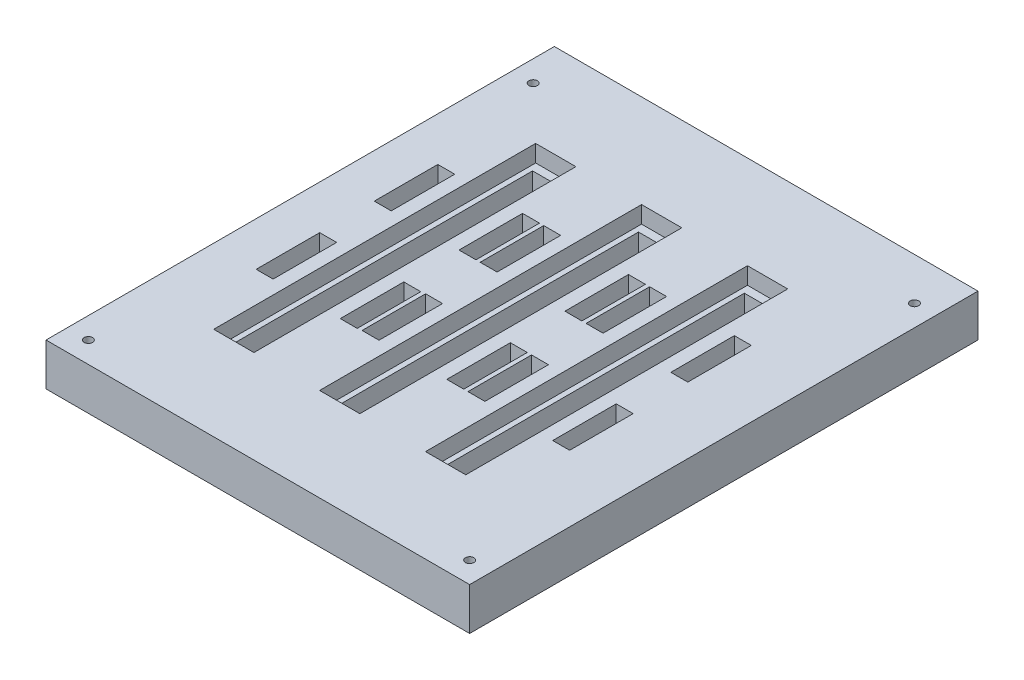
SolidWorks part; units mm, degrees
ref_plane "Front Plane" through (0, 0, 0) normal (0, 0, 1) x (1, 0, 0)
ref_plane "Top Plane" through (0, 0, 0) normal (0, 1, 0) x (1, 0, 0)
ref_plane "Right Plane" through (0, 0, 0) normal (1, 0, 0) x (0, 0, -1)
sketch "Sketch2" plane through (0, 0, 0) normal (0, 1, 0) x (1, 0, 0)
  line L0 (0, -60) -> (0, -36) construction
  line L1 (-50, -60) -> (50, -60)
  line L2 (-50, -60) -> (-50, 60)
  line L3 (-50, 60) -> (50, 60)
  line L4 (50, -60) -> (50, 60)
  line L5 (-50, -60) -> (-6.1463, -7.3755) construction
  line L6 (-50, 60) -> (-6.1463, 7.3755) construction
  line L7 (18.8537, 36) -> (25.8537, 36)
  line L8 (-6.1463, -36) -> (0.8537, -36)
  line L9 (-6.1463, -36) -> (-6.1463, 36)
  line L10 (-6.1463, 36) -> (0.8537, 36)
  line L11 (0.8537, -36) -> (0.8537, 36)
  line L12 (-50, 0) -> (50, 0) construction
  line L14 (25.8537, -36) -> (25.8537, 36)
  line L15 (18.8537, -36) -> (25.8537, -36)
  line L16 (18.8537, -36) -> (18.8537, 36)
  line L17 (-31.1463, 36) -> (-24.1463, 36)
  line L18 (-24.1463, -36) -> (-24.1463, 36)
  line L19 (-31.1463, -36) -> (-24.1463, -36)
  line L20 (-31.1463, -36) -> (-31.1463, 36)
  line L21 (0, 36) -> (0, 60) construction
  line L22 (0.8537, 1.0245) -> (50, 60) construction
  line L23 (0.8537, -1.0245) -> (50, -60) construction
  point P0 (0, 0)
  point P8 (0, 0)
  dimension "D1" = 120
  dimension "D2" = 100
  dimension "D3" = 72
  dimension "D4" = 7
  dimension "D7" = 18
  dimension "D8" = 18
  dimension "D5" = 2
  dimension "D6" = 2
extrude "Boss-Extrude1" add sketch "Sketch2" along normal blind 10
sketch "Sketch3" plane through (0, 10, 0) normal (0, 1, 0) x (1, 0, 0)
  line L0 (-24.1463, 36) -> (-6.1463, 36) construction
  line L1 (0.8537, 36) -> (18.8537, 36) construction
  line L2 (-24.1463, -36) -> (-6.1463, -36) construction
  line L3 (-24.1463, -36) -> (-24.1463, 36) construction
  line L4 (0.8537, -36) -> (18.8537, -36) construction
  line L5 (-17.6463, 36) -> (-17.6463, -36) construction
  line L6 (-31.1463, 36) -> (-45.1855, 36) construction
  line L7 (-31.1463, -36) -> (-45.1855, -36) construction
  line L8 (-37.6463, -36) -> (-37.6463, 36) construction
  line L9 (-31.1463, 36) -> (-31.1463, -36) construction
  line L10 (-12.6463, 36) -> (-12.6463, -36) construction
  line L11 (12.3537, 36) -> (12.3537, -36) construction
  line L12 (7.3537, 36) -> (7.3537, -36) construction
  line L13 (25.8537, 36) -> (44.8483, 36) construction
  line L14 (25.8537, -36) -> (46.6467, -36) construction
  line L15 (32.3537, 36) -> (32.3537, -36) construction
  line L16 (18.8537, 36) -> (18.8537, -36) construction
  line L17 (0.8537, -36) -> (0.8537, 36) construction
  line L18 (-6.1463, 36) -> (-6.1463, -36) construction
  line L19 (25.8537, -36) -> (25.8537, 36) construction
  line L20 (-37.6463, 14.6352) -> (32.3537, 14.6352) construction
  line L25 (-7.3963, -38.0209) -> (2.1037, -38.0209)
  line L26 (-19.6463, -20.8942) -> (-15.6463, -20.8942)
  line L27 (-37.6463, -13.2466) -> (32.3537, -13.2466) construction
  line L28 (-19.6463, -20.8942) -> (-19.6463, -5.8942)
  line L29 (-19.6463, -5.8942) -> (-15.6463, -5.8942)
  line L30 (-15.6463, -20.8942) -> (-15.6463, -5.8942)
  line L31 (-19.6463, -20.8942) -> (-15.6463, -5.8942) construction
  line L32 (-19.6463, -5.8942) -> (-15.6463, -20.8942) construction
  line L33 (-19.6463, 22.1352) -> (-15.6463, 22.1352)
  line L34 (-19.6463, 22.1352) -> (-19.6463, 7.1352)
  line L35 (-19.6463, 7.1352) -> (-15.6463, 7.1352)
  line L36 (-15.6463, 22.1352) -> (-15.6463, 7.1352)
  line L37 (-19.6463, 22.1352) -> (-15.6463, 7.1352) construction
  line L38 (-19.6463, 7.1352) -> (-15.6463, 22.1352) construction
  line L39 (-39.6463, 7.1352) -> (-35.6463, 7.1352)
  line L40 (-39.6463, 7.1352) -> (-39.6463, 22.1352)
  line L41 (-39.6463, 22.1352) -> (-35.6463, 22.1352)
  line L42 (-35.6463, 7.1352) -> (-35.6463, 22.1352)
  line L43 (-39.6463, 7.1352) -> (-35.6463, 22.1352) construction
  line L44 (-39.6463, 22.1352) -> (-35.6463, 7.1352) construction
  line L45 (-39.6463, -20.7466) -> (-35.6463, -20.7466)
  line L46 (-39.6463, -20.7466) -> (-39.6463, -5.7466)
  line L47 (-39.6463, -5.7466) -> (-35.6463, -5.7466)
  line L48 (-35.6463, -20.7466) -> (-35.6463, -5.7466)
  line L49 (-39.6463, -20.7466) -> (-35.6463, -5.7466) construction
  line L50 (-39.6463, -5.7466) -> (-35.6463, -20.7466) construction
  line L51 (-14.6463, -20.7466) -> (-10.6463, -20.7466)
  line L52 (-14.6463, -20.7466) -> (-14.6463, -5.7466)
  line L53 (-14.6463, -5.7466) -> (-10.6463, -5.7466)
  line L54 (-10.6463, -20.7466) -> (-10.6463, -5.7466)
  line L55 (-14.6463, -20.7466) -> (-10.6463, -5.7466) construction
  line L56 (-14.6463, -5.7466) -> (-10.6463, -20.7466) construction
  line L57 (-14.6463, 7.1352) -> (-10.6463, 7.1352)
  line L58 (-14.6463, 7.1352) -> (-14.6463, 22.1352)
  line L59 (-14.6463, 22.1352) -> (-10.6463, 22.1352)
  line L60 (-10.6463, 7.1352) -> (-10.6463, 22.1352)
  line L61 (-14.6463, 7.1352) -> (-10.6463, 22.1352) construction
  line L62 (-14.6463, 22.1352) -> (-10.6463, 7.1352) construction
  line L63 (5.3537, 7.1352) -> (9.3537, 7.1352)
  line L64 (5.3537, 7.1352) -> (5.3537, 22.1352)
  line L65 (5.3537, 22.1352) -> (9.3537, 22.1352)
  line L66 (9.3537, 7.1352) -> (9.3537, 22.1352)
  line L67 (5.3537, 7.1352) -> (9.3537, 22.1352) construction
  line L68 (5.3537, 22.1352) -> (9.3537, 7.1352) construction
  line L69 (10.3537, 7.1352) -> (14.3537, 7.1352)
  line L70 (10.3537, 7.1352) -> (10.3537, 22.1352)
  line L71 (10.3537, 22.1352) -> (14.3537, 22.1352)
  line L72 (14.3537, 7.1352) -> (14.3537, 22.1352)
  line L73 (10.3537, 7.1352) -> (14.3537, 22.1352) construction
  line L74 (10.3537, 22.1352) -> (14.3537, 7.1352) construction
  line L75 (10.3537, -20.7466) -> (14.3537, -20.7466)
  line L76 (10.3537, -20.7466) -> (10.3537, -5.7466)
  line L77 (10.3537, -5.7466) -> (14.3537, -5.7466)
  line L78 (14.3537, -20.7466) -> (14.3537, -5.7466)
  line L79 (10.3537, -20.7466) -> (14.3537, -5.7466) construction
  line L80 (10.3537, -5.7466) -> (14.3537, -20.7466) construction
  line L81 (5.3537, -20.7466) -> (9.3537, -20.7466)
  line L82 (5.3537, -20.7466) -> (5.3537, -5.7466)
  line L83 (5.3537, -5.7466) -> (9.3537, -5.7466)
  line L84 (9.3537, -20.7466) -> (9.3537, -5.7466)
  line L85 (5.3537, -20.7466) -> (9.3537, -5.7466) construction
  line L86 (5.3537, -5.7466) -> (9.3537, -20.7466) construction
  line L87 (30.3537, -20.7466) -> (34.3537, -20.7466)
  line L88 (30.3537, -20.7466) -> (30.3537, -5.7466)
  line L89 (30.3537, -5.7466) -> (34.3537, -5.7466)
  line L90 (34.3537, -20.7466) -> (34.3537, -5.7466)
  line L91 (30.3537, -20.7466) -> (34.3537, -5.7466) construction
  line L92 (30.3537, -5.7466) -> (34.3537, -20.7466) construction
  line L93 (30.3537, 7.1352) -> (34.3537, 7.1352)
  line L94 (30.3537, 7.1352) -> (30.3537, 22.1352)
  line L95 (30.3537, 22.1352) -> (34.3537, 22.1352)
  line L96 (34.3537, 7.1352) -> (34.3537, 22.1352)
  line L97 (30.3537, 7.1352) -> (34.3537, 22.1352) construction
  line L98 (30.3537, 22.1352) -> (34.3537, 7.1352) construction
  line L99 (-32.3963, -38.0209) -> (-22.8963, -38.0209)
  line L100 (-32.3963, -38.0209) -> (-32.3963, 37.9791)
  line L101 (-32.3963, 37.9791) -> (-22.8963, 37.9791)
  line L102 (-22.8963, -38.0209) -> (-22.8963, 37.9791)
  line L103 (-7.3963, -38.0209) -> (-7.3963, 37.9791)
  line L104 (-7.3963, 37.9791) -> (2.1037, 37.9791)
  line L105 (2.1037, -38.0209) -> (2.1037, 37.9791)
  line L106 (17.6037, -38.0209) -> (27.1037, -38.0209)
  line L107 (17.6037, -38.0209) -> (17.6037, 37.9791)
  line L108 (17.6037, 37.9791) -> (27.1037, 37.9791)
  line L109 (27.1037, -38.0209) -> (27.1037, 37.9791)
  line L110 (-24.1463, 36) -> (-31.1463, 36) construction
  point P51 (-17.6463, 0)
  point P52 (-17.6463, -13.3942)
  point P61 (-17.6463, 14.6352)
  point P74 (-12.6463, -13.2466)
  point P79 (-12.6463, 14.6352)
  point P84 (7.3537, 14.6352)
  point P89 (12.3537, 14.6352)
  point P94 (12.3537, -13.2466)
  point P99 (7.3537, -13.2466)
  dimension "D1" = 6.5
  dimension "D2" = 6.5
  dimension "D3" = 6.5
  dimension "D4" = 6.5
  dimension "D5" = 6.5
  dimension "D6" = 6.5
  dimension "D7" = 15
  dimension "D8" = 15
  dimension "D9" = 4
  dimension "D10" = 4
  dimension "D11" = 15
  dimension "D12" = 15
  dimension "D13" = 15
  dimension "D14" = 15
  dimension "D15" = 15
  dimension "D16" = 15
  dimension "D17" = 15
  dimension "D18" = 15
  dimension "D19" = 15
  dimension "D20" = 15
  dimension "D21" = 4
  dimension "D22" = 4
  dimension "D23" = 4
  dimension "D24" = 4
  dimension "D25" = 4
  dimension "D26" = 4
  dimension "D27" = 4
  dimension "D28" = 4
  dimension "D29" = 4
  dimension "D30" = 4
  dimension "D31" = 76
  dimension "D32" = 9.5
  dimension "D33" = 76
  dimension "D34" = 9.5
  dimension "D35" = 9.5
  dimension "D36" = 76
  dimension "D37" = 1.25
  dimension "D38" = 1.25
  dimension "D39" = 1.25
  dimension "D40" = 1.9791
  dimension "D41" = 1.9791
extrude "Cut-Extrude1" cut sketch "Sketch3" against normal blind 4
sketch "Sketch7" plane through (0, 0, 0) normal (0, -1, 0) x (1, 0, 0)
  line L0 (50, 60) -> (50, -60) construction
  line L1 (50, -60) -> (-50, -60) construction
  line L2 (-50, -60) -> (-50, 60) construction
  line L3 (-50, 60) -> (50, 60) construction
  circle A0 centre (45, -50) radius 2
  circle A1 centre (-45, -50) radius 2
  circle A2 centre (-45, 55) radius 2
  circle A3 centre (45, 55) radius 2
  dimension "D1" = 5
  dimension "D2" = 10
  dimension "D3" = 4
  dimension "D4" = 10
  dimension "D5" = 5
  dimension "D6" = 4
  dimension "D7" = 5
  dimension "D8" = 5
  dimension "D9" = 5
  dimension "D10" = 5
  dimension "D11" = 4
  dimension "D12" = 4
extrude "Cut-Extrude4" cut sketch "Sketch7" against normal blind 5
sketch "Sketch8" plane through (0, 5, 0) normal (0, -1, 0) x (-1, 0, 0)
  circle A0 centre (-45, 50) radius 1
  circle A1 centre (45, 50) radius 1
  circle A2 centre (45, -55) radius 1
  circle A3 centre (-45, -55) radius 1
  dimension "D1" = 2
  dimension "D2" = 2
  dimension "D3" = 2
  dimension "D4" = 2
extrude "Cut-Extrude5" cut sketch "Sketch8" against normal blind 5
